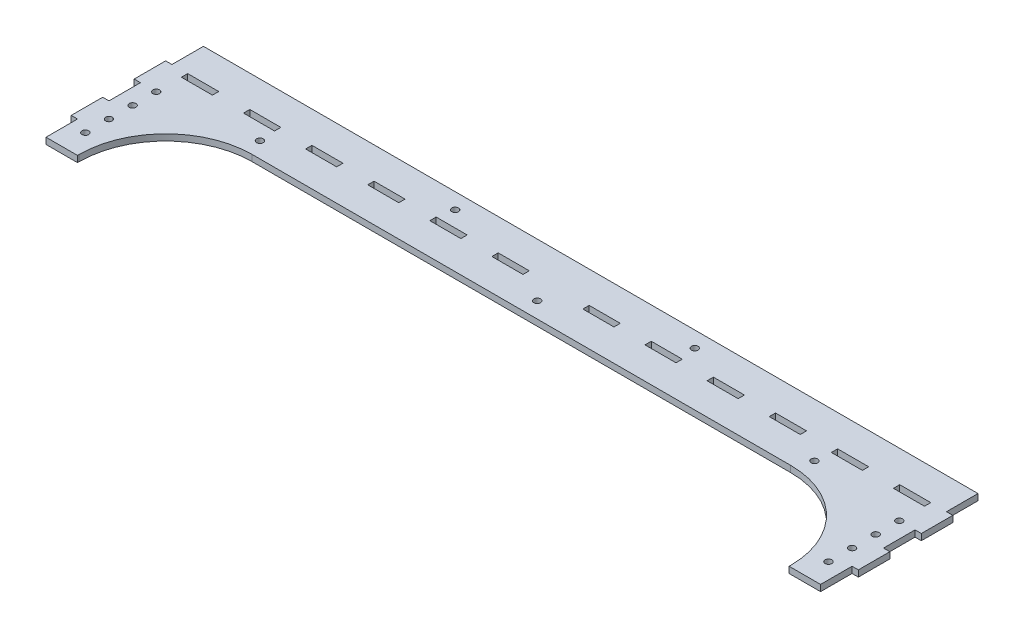
SolidWorks part; units mm, degrees
ref_plane "Front Plane" through (0, 0, 0) normal (0, 0, 1) x (1, 0, 0)
ref_plane "Top Plane" through (0, 0, 0) normal (0, 1, 0) x (1, 0, 0)
ref_plane "Right Plane" through (0, 0, 0) normal (1, 0, 0) x (0, 0, -1)
sketch "Sketch1" plane through (0, 0, 0) normal (0, 1, 0) x (1, 0, 0)
  line L0 (0, -24.6267) -> (0, 100.5806) construction
  line L1 (4, 0) -> (4, 20)
  line L2 (4, 20) -> (0, 20)
  line L3 (0, 20) -> (0, 40)
  line L4 (0, 40) -> (4, 40)
  line L5 (4, 40) -> (4, 60)
  line L6 (4, 60) -> (0, 60)
  line L7 (0, 60) -> (0, 80)
  line L8 (0, 80) -> (4, 80)
  line L9 (4, 80) -> (4, 100)
  line L10 (0, 0) -> (4, 0) construction
  line L11 (4, 0) -> (24, 0)
  line L12 (24, 0) -> (24, 1)
  line L13 (79, 56) -> (421, 56)
  line L16 (251.0496, 76) -> (-35.0505, 76) construction
  line L17 (14, 0) -> (14, 49.3314) construction
  line L18 (53.45, 76) -> (53.45, 80)
  line L19 (14, 76) -> (33.725, 76)
  line L20 (14, 76) -> (14, 80)
  line L21 (14, 80) -> (33.725, 80)
  line L22 (33.725, 76) -> (33.725, 80)
  line L23 (53.45, 76) -> (73.175, 76)
  line L24 (73.175, 76) -> (73.175, 80)
  line L25 (53.45, 80) -> (73.175, 80)
  line L26 (92.9, 76) -> (92.9, 80)
  line L27 (92.9, 76) -> (112.625, 76)
  line L28 (112.625, 76) -> (112.625, 80)
  line L29 (92.9, 80) -> (112.625, 80)
  line L30 (132.35, 76) -> (132.35, 80)
  line L31 (132.35, 76) -> (152.075, 76)
  line L32 (152.075, 76) -> (152.075, 80)
  line L33 (132.35, 80) -> (152.075, 80)
  line L34 (171.8, 76) -> (171.8, 80)
  line L35 (171.8, 76) -> (191.525, 76)
  line L36 (191.525, 76) -> (191.525, 80)
  line L37 (171.8, 80) -> (191.525, 80)
  line L38 (211.25, 76) -> (211.25, 80)
  line L39 (211.25, 76) -> (230.975, 76)
  line L40 (230.975, 76) -> (230.975, 80)
  line L41 (211.25, 80) -> (230.975, 80)
  line L42 (228.5555, 90) -> (146.8646, 90) construction
  line L43 (250, 56) -> (250, 140.3677) construction
  line L53 (4, 100) -> (250, 100)
  line L54 (271.4445, 90) -> (353.1354, 90) construction
  line L55 (486, 0) -> (486, 49.3314) construction
  line L56 (248.9504, 76) -> (535.0505, 76) construction
  line L57 (500, 0) -> (496, 0) construction
  line L58 (500, -24.6267) -> (500, 100.5806) construction
  line L59 (250, 100) -> (496, 100)
  line L60 (288.75, 80) -> (269.025, 80)
  line L61 (269.025, 76) -> (269.025, 80)
  line L62 (288.75, 76) -> (269.025, 76)
  line L63 (288.75, 76) -> (288.75, 80)
  line L64 (328.2, 80) -> (308.475, 80)
  line L65 (308.475, 76) -> (308.475, 80)
  line L66 (328.2, 76) -> (308.475, 76)
  line L67 (328.2, 76) -> (328.2, 80)
  line L68 (367.65, 80) -> (347.925, 80)
  line L69 (347.925, 76) -> (347.925, 80)
  line L70 (367.65, 76) -> (347.925, 76)
  line L71 (367.65, 76) -> (367.65, 80)
  line L72 (407.1, 80) -> (387.375, 80)
  line L73 (387.375, 76) -> (387.375, 80)
  line L74 (407.1, 76) -> (387.375, 76)
  line L75 (407.1, 76) -> (407.1, 80)
  line L76 (446.55, 80) -> (426.825, 80)
  line L77 (426.825, 76) -> (426.825, 80)
  line L78 (446.55, 76) -> (426.825, 76)
  line L79 (466.275, 76) -> (466.275, 80)
  line L80 (486, 80) -> (466.275, 80)
  line L81 (486, 76) -> (486, 80)
  line L82 (486, 76) -> (466.275, 76)
  line L83 (446.55, 76) -> (446.55, 80)
  line L84 (476, 0) -> (476, 1)
  line L85 (496, 0) -> (476, 0)
  line L86 (496, 80) -> (496, 100)
  line L87 (500, 80) -> (496, 80)
  line L88 (500, 60) -> (500, 80)
  line L89 (496, 60) -> (500, 60)
  line L90 (496, 40) -> (496, 60)
  line L91 (500, 40) -> (496, 40)
  line L92 (500, 20) -> (500, 40)
  line L93 (496, 20) -> (500, 20)
  line L94 (496, 0) -> (496, 20)
  line L95 (-5.4693, 37.5) -> (40.2804, 37.5) construction
  line L96 (50.2122, 66) -> (162.9928, 66) construction
  circle A0 centre (14, 15) radius 2.125
  circle A1 centre (14, 30) radius 2.125
  circle A10 centre (173.885, 90) radius 2.125
  circle A11 centre (326.115, 90) radius 2.125
  circle A12 centre (486, 30) radius 2.125
  circle A13 centre (486, 15) radius 2.125
  arc A14 (476, 1) -> (421, 56) centre (421, 1) ccw
  arc A15 (24, 1) -> (79, 56) centre (79, 1) cw
  circle A16 centre (14, 60) radius 2.125
  circle A17 centre (14, 45) radius 2.125
  circle A18 centre (486, 45) radius 2.125
  circle A19 centre (486, 60) radius 2.125
  circle A20 centre (73.88, 66) radius 2.125
  circle A21 centre (426.12, 66) radius 2.125
  circle A22 centre (250, 66) radius 2.125
  point P61 (250, 100)
  point P62 (476, 56)
  point P112 (24, 56)
  dimension "D8" = 4.25
  dimension "D14" = 4.25
  dimension "D17" = 10
  dimension "D19" = 73.88
  dimension "D15" = 55
  dimension "D1" = 20
  dimension "D2" = 44
  dimension "D3" = 4
  dimension "D4" = 20
  dimension "D5" = 246
  dimension "D6" = 100
  dimension "D7" = 20
  dimension "D9" = 15
  dimension "D10" = 15
  dimension "D11" = 10
  dimension "D12" = 19.725
  dimension "D13" = 4
  dimension "D16" = 7.5
  dimension "D18" = 6
extrude "Boss-Extrude1" add sketch "Sketch1" along normal blind 4
